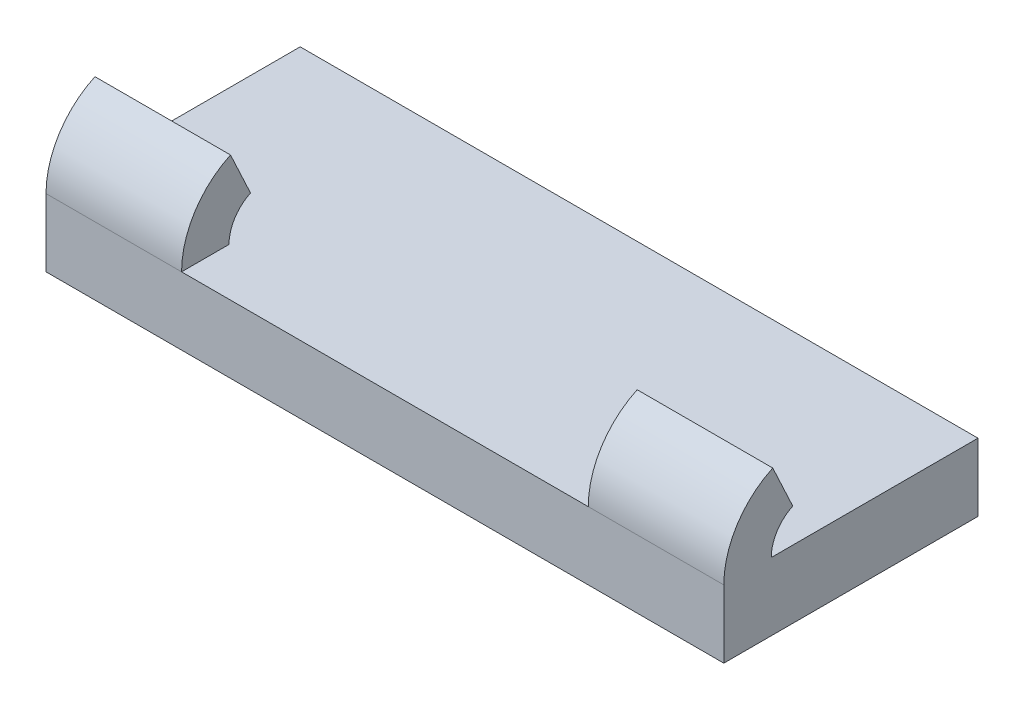
SolidWorks part; units mm, degrees
ref_plane "Front Plane" through (0, 0, 0) normal (0, 0, 1) x (1, 0, 0)
ref_plane "Top Plane" through (0, 0, 0) normal (0, 1, 0) x (1, 0, 0)
ref_plane "Right Plane" through (0, 0, 0) normal (1, 0, 0) x (0, 0, -1)
sketch "Sketch1" plane through (0, 0, 0) normal (0, 1, 0) x (1, 0, 0)
  line L1 (0, 0) -> (50.8, 0)
  line L2 (0, 0) -> (0, -19.05)
  line L3 (0, -19.05) -> (50.8, -19.05)
  line L4 (50.8, 0) -> (50.8, -19.05)
  dimension "D1" = 19.05
  dimension "D2" = 50.8
extrude "Boss-Extrude1" add sketch "Sketch1" along normal blind 5.08
sketch "Sketch2" plane through (0, 5.08, 0) normal (0, 1, 0) x (1, 0, 0)
  line L0 (0, 0) -> (0, -19.05) construction
  line L1 (0, -15.494) -> (10.16, -15.494)
  line L2 (0, -15.494) -> (0, -19.05)
  line L3 (0, -19.05) -> (10.16, -19.05)
  line L4 (10.16, -15.494) -> (10.16, -19.05)
  line L5 (50.8, -19.05) -> (50.8, 0) construction
  line L6 (50.8, -15.494) -> (40.64, -15.494)
  line L7 (50.8, -15.494) -> (50.8, -19.05)
  line L8 (50.8, -19.05) -> (40.64, -19.05)
  line L9 (40.64, -15.494) -> (40.64, -19.05)
  line L10 (0, -12.7) -> (50.8, -12.7) construction
  line L11 (0, -19.05) -> (50.8, -19.05) construction
  dimension "D1" = 2.794
  dimension "D2" = 2.794
  dimension "D3" = 0
  dimension "D4" = 3.556
  dimension "D5" = 10.16
  dimension "D6" = 10.16
revolve "Revolve1" add sketch "Sketch2" angle 65 about L10
